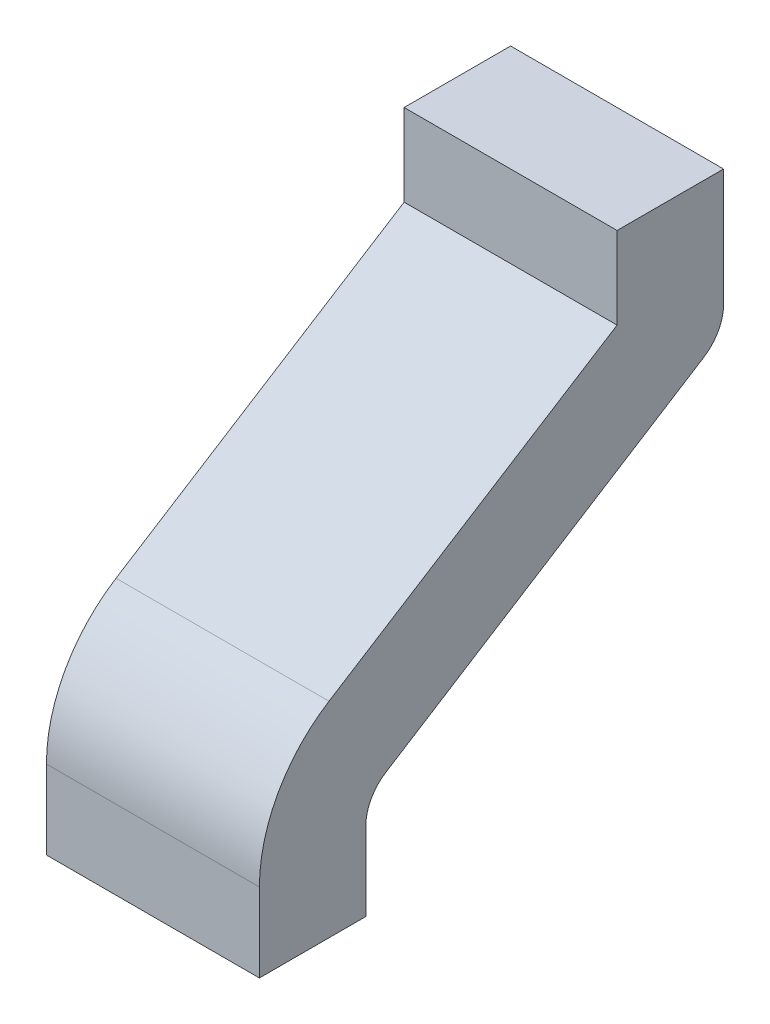
SolidWorks part; units mm, degrees
ref_plane "Plan de face" through (0, 0, 0) normal (0, 0, 1) x (1, 0, 0)
ref_plane "Plan de dessus" through (0, 0, 0) normal (0, 1, 0) x (1, 0, 0)
ref_plane "Plan de droite" through (0, 0, 0) normal (1, 0, 0) x (0, 0, -1)
sketch "Esquisse1" plane through (0, 0, 0) normal (-1, 0, 0) x (0, 0, 1)
  line L1 (0.65, 4) -> (0.65, 4.185)
  line L3 (1.1, 5.1) -> (-2.0714, 5.1) construction
  line L4 (0.6033, 4.2696) -> (-0.143, 4.7402)
  line L5 (-0.1897, 4.8248) -> (-0.1897, 5.1)
  line L6 (0.9, 4) -> (0.9, 4.185)
  line L7 (0.7367, 4.4811) -> (0.0603, 4.9075)
  line L8 (0.0603, 4.9075) -> (0.0603, 5.1)
  line L9 (-0.1897, 5.1) -> (0.0603, 5.1)
  line L10 (0.65, 4) -> (0.9, 4)
  line L11 (0.6033, 4.2696) -> (-0.1897, 4.7696) construction
  line L12 (-0.1897, 4.7696) -> (-0.1897, 5.1) construction
  arc A0 (0.6033, 4.2696) -> (0.65, 4.185) centre (0.55, 4.185) cw
  arc A1 (0.7367, 4.4811) -> (0.9, 4.185) centre (0.55, 4.185) cw
  arc A2 (-0.143, 4.7402) -> (-0.1897, 4.8248) centre (-0.0897, 4.8248) cw
  dimension "D2" = 0.1
  dimension "D4" = 0.1
  dimension "D3" = 0.25
extrude "Boss.-Extru.1" add sketch "Esquisse1" along normal blind 0.5
